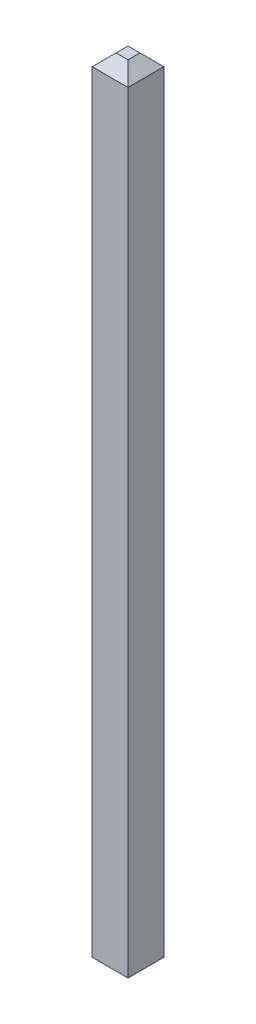
SolidWorks part; units mm, degrees
ref_plane "Front Plane" through (0, 0, 0) normal (0, 0, 1) x (1, 0, 0)
ref_plane "Top Plane" through (0, 0, 0) normal (0, 1, 0) x (1, 0, 0)
ref_plane "Right Plane" through (0, 0, 0) normal (1, 0, 0) x (0, 0, -1)
sketch "Sketch1" plane through (0, 0, 0) normal (0, 1, 0) x (1, 0, 0)
  line L0 (0, 1.25) -> (0, -1.25) construction
  line L1 (-2.75, 1.25) -> (2.75, 1.25)
  line L2 (-2.75, 1.25) -> (-2.75, -1.25)
  line L3 (-2.75, -1.25) -> (2.75, -1.25)
  line L4 (2.75, 1.25) -> (2.75, -1.25)
  dimension "D1" = 5.5
  dimension "D2" = 2.5
extrude "Boss-Extrude1" add sketch "Sketch1" along normal blind 2.5
sketch "Sketch2" plane through (0, 2.5, 0) normal (0, 1, 0) x (1, 0, 0)
  line L0 (0, 1.25) -> (0, -1.25) construction
  line L1 (2.75, 1.25) -> (-2.75, 1.25) construction
  line L2 (-2.75, -1.25) -> (2.75, -1.25) construction
  line L3 (0, 0) -> (-2.75, 0) construction
  line L4 (-2.75, 1.25) -> (-2.75, -1.25) construction
  line L5 (0, 0) -> (2.75, 0) construction
  line L6 (2.75, -1.25) -> (2.75, 1.25) construction
  line L7 (-1.25, 0.3) -> (-1.25, -0.3) construction
  line L8 (-1.55, 0.3) -> (-0.95, 0.3)
  line L9 (-1.55, 0.3) -> (-1.55, -0.3)
  line L10 (-1.55, -0.3) -> (-0.95, -0.3)
  line L11 (-0.95, 0.3) -> (-0.95, -0.3)
  point P18 (-1.25, 0)
  dimension "D1" = 1.25
  dimension "D2" = 0.6
  dimension "D3" = 0.6
extrude "Boss-Extrude2" add sketch "Sketch2" along normal blind 2.5 and the other way blind 10.8
chamfer "Chamfer1" distance 0.2 angle 45 8 edges at (-1.25, 5, -0.3) (-1.55, 5, 0) (-1.25, 5, 0.3) (-0.95, 5, 0) (-1.55, -8.3, 0) (-1.25, -8.3, -0.3) (-0.95, -8.3, 0) (-1.25, -8.3, 0.3)
mirror "Mirror1" about plane through (0, 0, 0) normal (1, 0, 0) of "Chamfer1", "Boss-Extrude2"
sketch "Sketch3" plane through (0, 2.5, 0) normal (0, 1, 0) x (1, 0, 0)
  line L1 (-1.55, -0.3) -> (-0.95, -0.3)
  line L2 (-1.55, -0.3) -> (-1.55, 0.3)
  line L3 (-1.55, 0.3) -> (-0.95, 0.3)
  line L4 (-0.95, -0.3) -> (-0.95, 0.3)
  line L5 (-6.1188, 5.7531) -> (6.1964, 5.7531)
  line L6 (-6.1188, 5.7531) -> (-6.1188, -4.8777)
  line L7 (-6.1188, -4.8777) -> (6.1964, -4.8777)
  line L8 (6.1964, 5.7531) -> (6.1964, -4.8777)
extrude "Cut-Extrude2" cut sketch "Sketch3" against normal blind 30 and the other way blind 10
